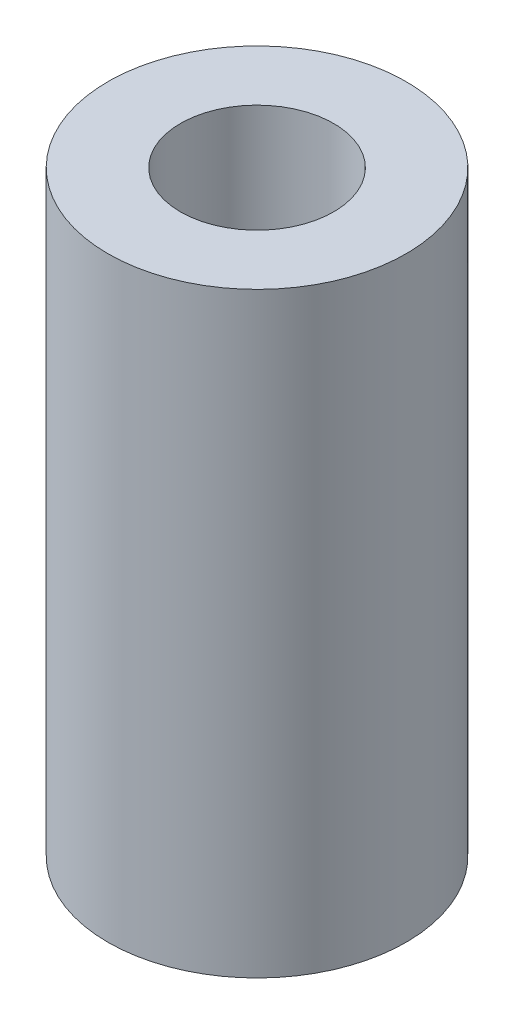
SolidWorks part; units mm, degrees
material "6061 Alloy"
ref_plane "Front Plane" through (0, 0, 0) normal (0, 0, 1) x (1, 0, 0)
ref_plane "Top Plane" through (0, 0, 0) normal (0, 1, 0) x (1, 0, 0)
ref_plane "Right Plane" through (0, 0, 0) normal (1, 0, 0) x (0, 0, -1)
sketch "Sketch1" plane through (0, 0, 0) normal (0, 1, 0) x (1, 0, 0)
  circle A0 centre (0, 0) radius 6.35
  circle A1 centre (0, 0) radius 3.2639
  dimension "D1" = 12.7
  dimension "D2" = 6.5278
extrude "Boss-Extrude1" add sketch "Sketch1" along normal blind 25.4
